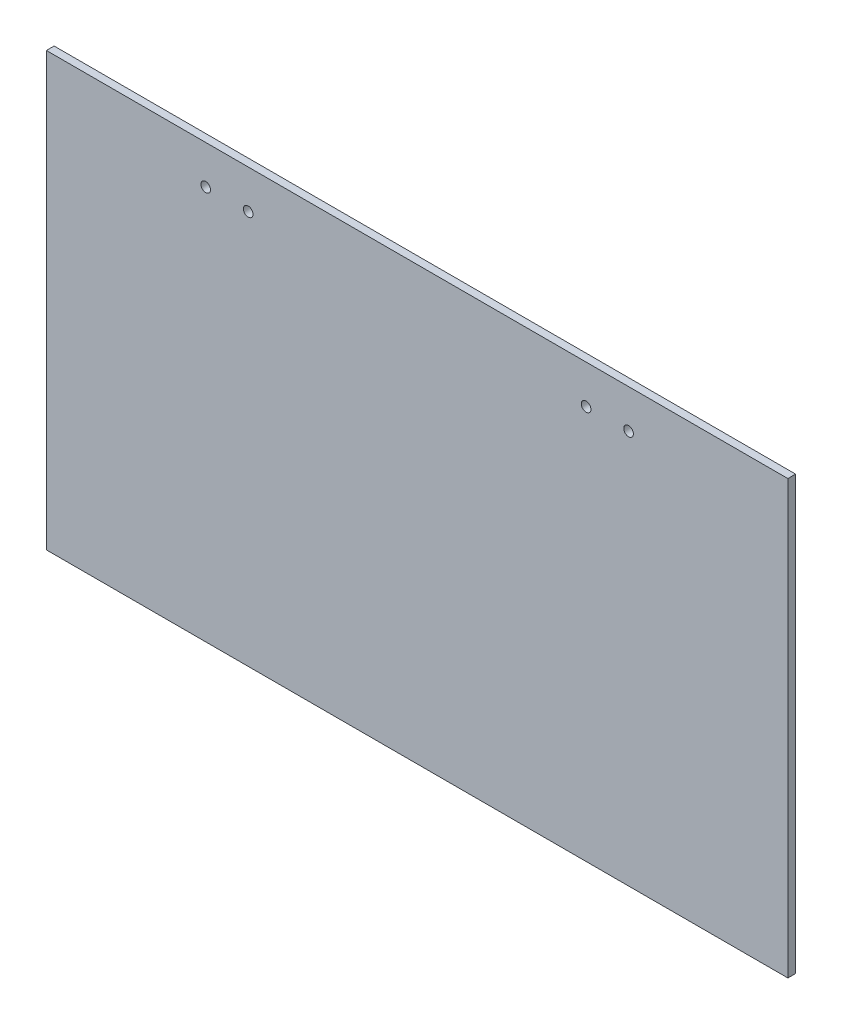
SolidWorks part; units mm, degrees
ref_plane "Front Plane" through (0, 0, 0) normal (0, 0, 1) x (1, 0, 0)
ref_plane "Top Plane" through (0, 0, 0) normal (0, 1, 0) x (1, 0, 0)
ref_plane "Right Plane" through (0, 0, 0) normal (1, 0, 0) x (0, 0, -1)
sketch "Sketch1" plane through (0, 0, 0) normal (0, 0, 1) x (1, 0, 0)
  line L1 (-152.4, -88.9) -> (152.4, -88.9)
  line L2 (-152.4, -88.9) -> (-152.4, 88.9)
  line L3 (-152.4, 88.9) -> (152.4, 88.9)
  line L4 (152.4, -88.9) -> (152.4, 88.9)
  line L5 (-152.4, -88.9) -> (152.4, 88.9) construction
  line L6 (-152.4, 88.9) -> (152.4, -88.9) construction
  point P0 (0, 0)
  dimension "D1" = 304.8
  dimension "D2" = 177.8
extrude "Boss-Extrude1" add sketch "Sketch1" along normal blind 3.175
sketch "Sketch2" plane through (0, 0, 3.175) normal (0, 0, 1) x (1, 0, 0)
  line L1 (-152.4, 88.9) -> (-152.4, -88.9) construction
  line L2 (152.4, -88.9) -> (152.4, 88.9) construction
  line L3 (152.4, 88.9) -> (-152.4, 88.9) construction
  line L4 (-152.4, 73.025) -> (152.4, 73.025) construction
  line L5 (-88.9, 73.025) -> (-88.9, 88.9) construction
  line L6 (-67.4688, 73.025) -> (-67.4688, 88.9) construction
  line L7 (0, 0) -> (0, 88.9) construction
  circle A0 centre (-86.9156, 73.025) radius 1.9844
  circle A1 centre (-69.4531, 73.025) radius 1.9844
  circle A2 centre (69.4531, 73.025) radius 1.9844
  circle A3 centre (86.9156, 73.025) radius 1.9844
  dimension "D3" = 3.9688
  dimension "D4" = 3.9688
  dimension "D2" = 15.875
  dimension "D5" = 21.4312
  dimension "D6" = 63.5
extrude "Cut-Extrude1" cut sketch "Sketch2" against normal through all
